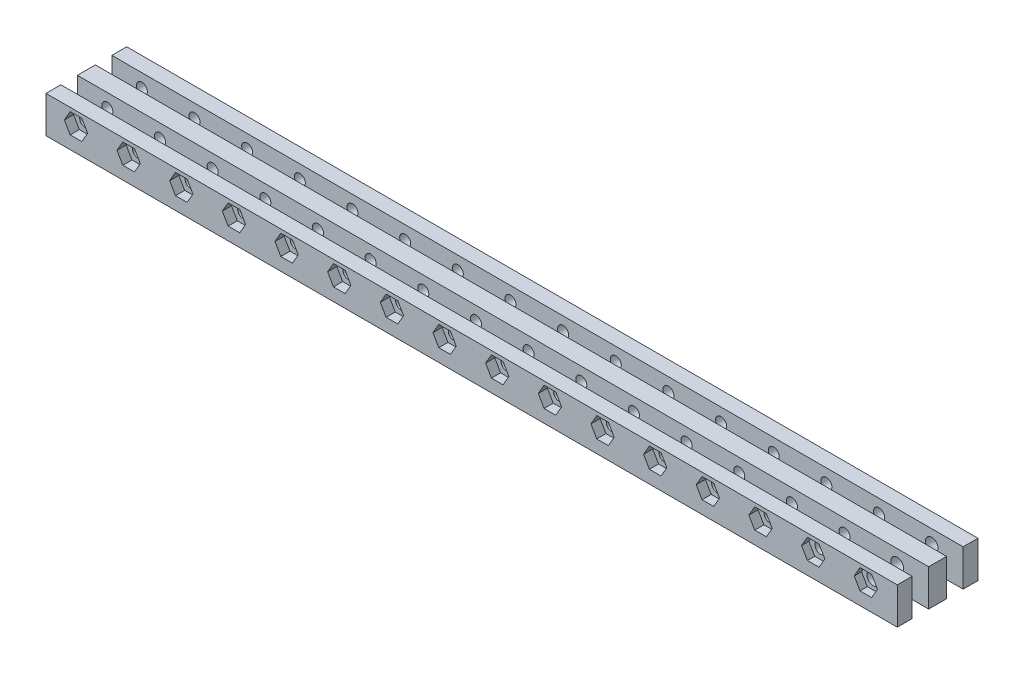
SolidWorks part; units mm, degrees
ref_plane "Front Plane" through (0, 0, 0) normal (0, 0, 1) x (1, 0, 0)
ref_plane "Top Plane" through (0, 0, 0) normal (0, 1, 0) x (1, 0, 0)
ref_plane "Right Plane" through (0, 0, 0) normal (1, 0, 0) x (0, 0, -1)
sketch "Sketch1" plane through (0, 0, 0) normal (0, 1, 0) x (1, 0, 0)
  line L1 (117.5, -11) -> (-117.5, -11)
  line L2 (117.5, -11) -> (117.5, 11)
  line L3 (117.5, 11) -> (-117.5, 11)
  line L4 (-117.5, -11) -> (-117.5, 11)
  line L5 (0, 11) -> (0, -11) construction
  line L6 (117.5, 0) -> (-117.5, 0) construction
  point P0 (0, 0)
  dimension "D1" = 235
  dimension "D2" = 22
extrude "Boss-Extrude1" add sketch "Sketch1" along normal blind 10
sketch "Sketch2" plane through (0, 10, 0) normal (0, 1, 0) x (1, 0, 0)
  line L0 (-117.5, 11) -> (-117.5, -11) construction
  line L1 (-117.5, -2.4504) -> (117.5, -2.4504)
  line L2 (-117.5, -2.4504) -> (-117.5, -6.9504)
  line L3 (-117.5, -6.9504) -> (117.5, -6.9504)
  line L4 (117.5, -2.4504) -> (117.5, -6.9504)
  line L5 (117.5, -11) -> (117.5, 11) construction
  line L6 (-117.5, 0) -> (108.3852, 0) construction
  line L7 (-117.5, -11) -> (117.5, -11) construction
  line L8 (117.5, 2.4504) -> (117.5, 6.9504)
  line L9 (-117.5, 2.4504) -> (-117.5, 6.9504)
  line L10 (-117.5, 2.4504) -> (117.5, 2.4504)
  line L11 (-117.5, 6.9504) -> (117.5, 6.9504)
  dimension "D1" = 4.5
extrude "Cut-Extrude1" cut sketch "Sketch2" against normal blind 6
sketch "Sketch3" plane through (0, 0, 11) normal (0, 0, 1) x (1, 0, 0)
  line L6 (-109.5, 6.25) -> (-103.1491, 6.25) construction
  line L7 (-117.5, 10) -> (117.5, 10) construction
  line L8 (-103.1491, 6.25) -> (-104.7369, 9)
  line L9 (-104.7369, 9) -> (-107.9123, 9)
  line L10 (-107.9123, 9) -> (-109.5, 6.25)
  line L11 (-109.5, 6.25) -> (-107.9123, 3.5)
  line L12 (-107.9123, 3.5) -> (-104.7369, 3.5)
  line L13 (-104.7369, 3.5) -> (-103.1491, 6.25)
  line L14 (-117.5, 10) -> (-117.5, 0) construction
  line L15 (-99.1491, 10) -> (-99.1491, 0) construction
  line L16 (-117.5, 0) -> (117.5, 0) construction
  line L17 (-95.1491, 6.25) -> (-93.5614, 9)
  line L18 (-93.5614, 3.5) -> (-95.1491, 6.25)
  line L19 (-90.386, 3.5) -> (-93.5614, 3.5)
  line L20 (-88.7983, 6.25) -> (-90.386, 3.5)
  line L21 (-90.386, 9) -> (-88.7983, 6.25)
  line L22 (-93.5614, 9) -> (-90.386, 9)
  line L23 (-84.7983, 10) -> (-84.7983, 0) construction
  line L24 (-70.4474, 10) -> (-70.4474, 0) construction
  line L25 (-60.0966, 6.25) -> (-66.4474, 6.25) construction
  line L26 (-76.0352, 9) -> (-79.2106, 9)
  line L27 (-79.2106, 9) -> (-80.7983, 6.25)
  line L28 (-80.7983, 6.25) -> (-79.2106, 3.5)
  line L29 (-79.2106, 3.5) -> (-76.0352, 3.5)
  line L30 (-76.0352, 3.5) -> (-74.4474, 6.25)
  line L31 (-74.4474, 6.25) -> (-76.0352, 9)
  line L32 (-64.8597, 3.5) -> (-66.4474, 6.25)
  line L33 (-61.6843, 3.5) -> (-64.8597, 3.5)
  line L34 (-60.0966, 6.25) -> (-61.6843, 3.5)
  line L35 (-61.6843, 9) -> (-60.0966, 6.25)
  line L36 (-64.8597, 9) -> (-61.6843, 9)
  line L37 (-66.4474, 6.25) -> (-64.8597, 9)
  line L38 (-80.7983, 6.25) -> (-74.4474, 6.25) construction
  line L39 (-31.3949, 6.25) -> (-37.7457, 6.25) construction
  line L52 (-47.3334, 9) -> (-50.5089, 9)
  line L53 (-50.5089, 9) -> (-52.0966, 6.25)
  line L54 (-52.0966, 6.25) -> (-50.5089, 3.5)
  line L55 (-50.5089, 3.5) -> (-47.3334, 3.5)
  line L56 (-47.3334, 3.5) -> (-45.7457, 6.25)
  line L57 (-45.7457, 6.25) -> (-47.3334, 9)
  line L58 (-36.158, 3.5) -> (-37.7457, 6.25)
  line L59 (-32.9826, 3.5) -> (-36.158, 3.5)
  line L60 (-31.3949, 6.25) -> (-32.9826, 3.5)
  line L61 (-32.9826, 9) -> (-31.3949, 6.25)
  line L62 (-36.158, 9) -> (-32.9826, 9)
  line L63 (-37.7457, 6.25) -> (-36.158, 9)
  line L64 (-27.3949, 10) -> (-27.3949, 0) construction
  line L65 (-23.3949, 6.25) -> (-17.044, 6.25) construction
  line L66 (26.0085, 6.25) -> (19.6577, 6.25) construction
  line L67 (5.3068, 6.25) -> (11.6577, 6.25) construction
  line L68 (15.6577, 10) -> (15.6577, 0) construction
  line L69 (30.0085, 10) -> (30.0085, 0) construction
  line L70 (44.3594, 10) -> (44.3594, 0) construction
  line L71 (54.7102, 6.25) -> (48.3594, 6.25) construction
  line L72 (-17.044, 6.25) -> (-18.6317, 9)
  line L73 (-18.6317, 9) -> (-21.8072, 9)
  line L74 (-21.8072, 9) -> (-23.3949, 6.25)
  line L75 (-23.3949, 6.25) -> (-21.8072, 3.5)
  line L76 (-21.8072, 3.5) -> (-18.6317, 3.5)
  line L77 (-18.6317, 3.5) -> (-17.044, 6.25)
  line L78 (-9.044, 6.25) -> (-7.4563, 9)
  line L79 (-7.4563, 3.5) -> (-9.044, 6.25)
  line L80 (-4.2809, 3.5) -> (-7.4563, 3.5)
  line L81 (-2.6932, 6.25) -> (-4.2809, 3.5)
  line L82 (-4.2809, 9) -> (-2.6932, 6.25)
  line L83 (-7.4563, 9) -> (-4.2809, 9)
  line L84 (10.07, 9) -> (6.8945, 9)
  line L85 (6.8945, 9) -> (5.3068, 6.25)
  line L86 (5.3068, 6.25) -> (6.8945, 3.5)
  line L87 (6.8945, 3.5) -> (10.07, 3.5)
  line L88 (10.07, 3.5) -> (11.6577, 6.25)
  line L89 (11.6577, 6.25) -> (10.07, 9)
  line L90 (21.2454, 3.5) -> (19.6577, 6.25)
  line L91 (24.4208, 3.5) -> (21.2454, 3.5)
  line L92 (26.0085, 6.25) -> (24.4208, 3.5)
  line L93 (24.4208, 9) -> (26.0085, 6.25)
  line L94 (21.2454, 9) -> (24.4208, 9)
  line L95 (19.6577, 6.25) -> (21.2454, 9)
  line L108 (38.7717, 9) -> (35.5962, 9)
  line L109 (35.5962, 9) -> (34.0085, 6.25)
  line L110 (34.0085, 6.25) -> (35.5962, 3.5)
  line L111 (35.5962, 3.5) -> (38.7717, 3.5)
  line L112 (38.7717, 3.5) -> (40.3594, 6.25)
  line L113 (40.3594, 6.25) -> (38.7717, 9)
  line L114 (49.9471, 3.5) -> (48.3594, 6.25)
  line L115 (53.1225, 3.5) -> (49.9471, 3.5)
  line L116 (54.7102, 6.25) -> (53.1225, 3.5)
  line L117 (53.1225, 9) -> (54.7102, 6.25)
  line L118 (49.9471, 9) -> (53.1225, 9)
  line L119 (48.3594, 6.25) -> (49.9471, 9)
  line L120 (58.7102, 10) -> (58.7102, 0) construction
  line L121 (62.7102, 6.25) -> (69.0611, 6.25) construction
  line L122 (73.0611, 10) -> (73.0611, 0) construction
  line L123 (69.0611, 6.25) -> (67.4734, 9)
  line L124 (67.4734, 9) -> (64.2979, 9)
  line L125 (64.2979, 9) -> (62.7102, 6.25)
  line L126 (62.7102, 6.25) -> (64.2979, 3.5)
  line L127 (64.2979, 3.5) -> (67.4734, 3.5)
  line L128 (67.4734, 3.5) -> (69.0611, 6.25)
  line L129 (77.0611, 6.25) -> (78.6488, 9)
  line L130 (78.6488, 3.5) -> (77.0611, 6.25)
  line L131 (81.8242, 3.5) -> (78.6488, 3.5)
  line L132 (83.4119, 6.25) -> (81.8242, 3.5)
  line L133 (81.8242, 9) -> (83.4119, 6.25)
  line L134 (78.6488, 9) -> (81.8242, 9)
  circle A0 centre (-106.3246, 6.25) radius 2.75 construction
  circle A1 centre (-63.272, 6.25) radius 2.75 construction
  circle A2 centre (-77.6229, 6.25) radius 2.75 construction
  circle A3 centre (-34.5703, 6.25) radius 2.75 construction
  circle A4 centre (-20.2195, 6.25) radius 2.75 construction
  circle A5 centre (22.8331, 6.25) radius 2.75 construction
  circle A6 centre (8.4823, 6.25) radius 2.75 construction
  circle A7 centre (51.5348, 6.25) radius 2.75 construction
  circle A8 centre (65.8857, 6.25) radius 2.75 construction
  dimension "D1" = 5.5
  dimension "D2" = 6.3509
  dimension "D3" = 1
  dimension "D4" = 8
  dimension "D5" = 4
  dimension "D6" = 4
  dimension "D7" = 4
  dimension "D8" = 4
extrude "Cut-Extrude3" cut sketch "Sketch3" against normal blind 2.5
sketch "Sketch8" plane through (0, 0, 11) normal (0, 0, 1) x (1, 0, 0)
  line L0 (-109.5, 6.25) -> (-103.1491, 6.25) construction
  line L2 (-106.3246, 9) -> (-106.3246, 3.5) construction
  line L3 (-104.7369, 9) -> (-107.9123, 9) construction
  line L4 (-107.9123, 3.5) -> (-104.7369, 3.5) construction
sketch "Sketch9" plane through (0, 0, 11) normal (0, 0, 1) x (1, 0, 0)
  line L0 (-109.5, 6.25) -> (-103.1491, 6.25) construction
  line L1 (-91.9737, 9) -> (-91.9737, 3.5) construction
  line L2 (-90.386, 9) -> (-93.5614, 9) construction
  line L3 (-93.5614, 3.5) -> (-90.386, 3.5) construction
  line L4 (-106.3246, 9) -> (-106.3246, 3.5) construction
  line L5 (-106.3246, 6.25) -> (-91.9737, 6.25) construction
  circle A0 centre (-106.3246, 6.25) radius 1.5
  circle A1 centre (-91.9737, 6.25) radius 1.5
  circle A2 centre (-77.6229, 6.25) radius 1.5
  circle A3 centre (-63.272, 6.25) radius 1.5
  circle A4 centre (-48.9212, 6.25) radius 1.5
  circle A5 centre (-34.5703, 6.25) radius 1.5
  circle A6 centre (-20.2195, 6.25) radius 1.5
  circle A7 centre (-5.8686, 6.25) radius 1.5
  circle A8 centre (8.4823, 6.25) radius 1.5
  circle A9 centre (22.8331, 6.25) radius 1.5
  circle A10 centre (37.184, 6.25) radius 1.5
  circle A11 centre (51.5348, 6.25) radius 1.5
  circle A12 centre (65.8857, 6.25) radius 1.5
  circle A13 centre (80.2365, 6.25) radius 1.5
  dimension "D1" = 14.3509
  dimension "D3" = 14.3509
  dimension "D2" = 14
extrude "Cut-Extrude4" cut sketch "Sketch9" against normal through all
sketch "草图1" plane through (0, 0, 0) normal (0, -1, 0) x (1, 0, 0)
  line L0 (117.5, 0) -> (-117.5, 0) construction
  line L1 (117.5, 11) -> (117.5, -11) construction
  line L2 (-117.5, -11) -> (-117.5, 11) construction
  line L3 (0, 11) -> (0, -11) construction
  line L4 (-117.5, 11) -> (117.5, 11) construction
  line L5 (117.5, -11) -> (-117.5, -11) construction
  circle A0 centre (97.8584, 6.2653) radius 1.9171
  circle A1 centre (97.8584, -6.2653) radius 1.9171
  circle A2 centre (-97.8584, -6.2653) radius 1.9171
  circle A3 centre (-97.8584, 6.2653) radius 1.9171
sketch "草图3" plane through (0, 0, 11) normal (0, 0, 1) x (1, 0, 0)
  circle A0 centre (80.2365, 6.25) radius 1.5
  circle A1 centre (94.5865, 6.25) radius 1.5019
  circle A2 centre (108.9365, 6.25) radius 1.717
  circle A3 centre (65.8857, 6.25) radius 1.5
  dimension "D1" = 14.35
  dimension "D2" = 14.35
extrude "切除-拉伸1" cut sketch "草图3" against normal through all
sketch "草图4" plane through (0, 0, 11) normal (0, 0, 1) x (1, 0, 0)
  line L0 (81.8242, 3.5) -> (83.4119, 6.25)
  line L1 (83.4119, 6.25) -> (81.8242, 9)
  line L2 (81.8242, 9) -> (78.6488, 9)
  line L3 (78.6488, 9) -> (77.0611, 6.25)
  line L4 (77.0611, 6.25) -> (78.6488, 3.5)
  line L5 (78.6488, 3.5) -> (81.8242, 3.5)
  line L6 (97.7619, 6.25) -> (96.1742, 9)
  line L7 (96.1742, 9) -> (92.9988, 9)
  line L8 (92.9988, 9) -> (91.4111, 6.25)
  line L9 (91.4111, 6.25) -> (92.9988, 3.5)
  line L10 (92.9988, 3.5) -> (96.1742, 3.5)
  line L11 (96.1742, 3.5) -> (97.7619, 6.25)
  line L12 (112.1119, 6.25) -> (110.5242, 9)
  line L13 (110.5242, 9) -> (107.3488, 9)
  line L14 (107.3488, 9) -> (105.7611, 6.25)
  line L15 (105.7611, 6.25) -> (107.3488, 3.5)
  line L16 (107.3488, 3.5) -> (110.5242, 3.5)
  line L17 (110.5242, 3.5) -> (112.1119, 6.25)
  dimension "D1" = 3
extrude "切除-拉伸2" cut sketch "草图4" against normal blind 2
sketch "草图6" plane through (0, 4, 0) normal (0, 1, 0) x (1, 0, 0)
  line L0 (-117.5, -6.9504) -> (117.5, -6.9504) construction
  line L1 (82.5, -6.9504) -> (117.5, -6.9504)
  line L2 (82.5, -6.9504) -> (82.5, -2.4504)
  line L3 (82.5, -2.4504) -> (117.5, -2.4504)
  line L4 (117.5, -6.9504) -> (117.5, -2.4504)
  line L5 (-117.5, 2.4504) -> (117.5, 2.4504) construction
  line L6 (82.5, 2.4504) -> (117.5, 2.4504)
  line L7 (82.5, 2.4504) -> (82.5, 6.9504)
  line L8 (82.5, 6.9504) -> (117.5, 6.9504)
  line L9 (117.5, 2.4504) -> (117.5, 6.9504)
  line L10 (117.5, -2.4504) -> (-117.5, -2.4504) construction
  line L11 (-117.5, -6.9504) -> (-82.5, -6.9504)
  line L12 (-117.5, -6.9504) -> (-117.5, -2.4504)
  line L13 (-117.5, -2.4504) -> (-82.5, -2.4504)
  line L14 (-82.5, -6.9504) -> (-82.5, -2.4504)
  line L15 (117.5, 6.9504) -> (-117.5, 6.9504) construction
  line L16 (-117.5, 2.4504) -> (-82.5, 2.4504)
  line L17 (-117.5, 2.4504) -> (-117.5, 6.9504)
  line L18 (-117.5, 6.9504) -> (-82.5, 6.9504)
  line L19 (-82.5, 2.4504) -> (-82.5, 6.9504)
  point P14 (82.5, 4.7004)
  dimension "D1" = 35
  dimension "D2" = 35
  dimension "D3" = 35
extrude "切除-拉伸3" cut sketch "草图6" against normal through all
sketch "草图9" plane through (0, 10, 0) normal (0, 1, 0) x (1, 0, 0)
  line L0 (-117.5, -11) -> (117.5, -11) construction
  line L1 (-117.5, 11) -> (-114.5, 11)
  line L2 (-117.5, 11) -> (-117.5, -11)
  line L3 (-117.5, -11) -> (-114.5, -11)
  line L4 (-114.5, 11) -> (-114.5, -11)
  dimension "D1" = 3
extrude "切除-拉伸4" cut sketch "草图9" against normal through all
